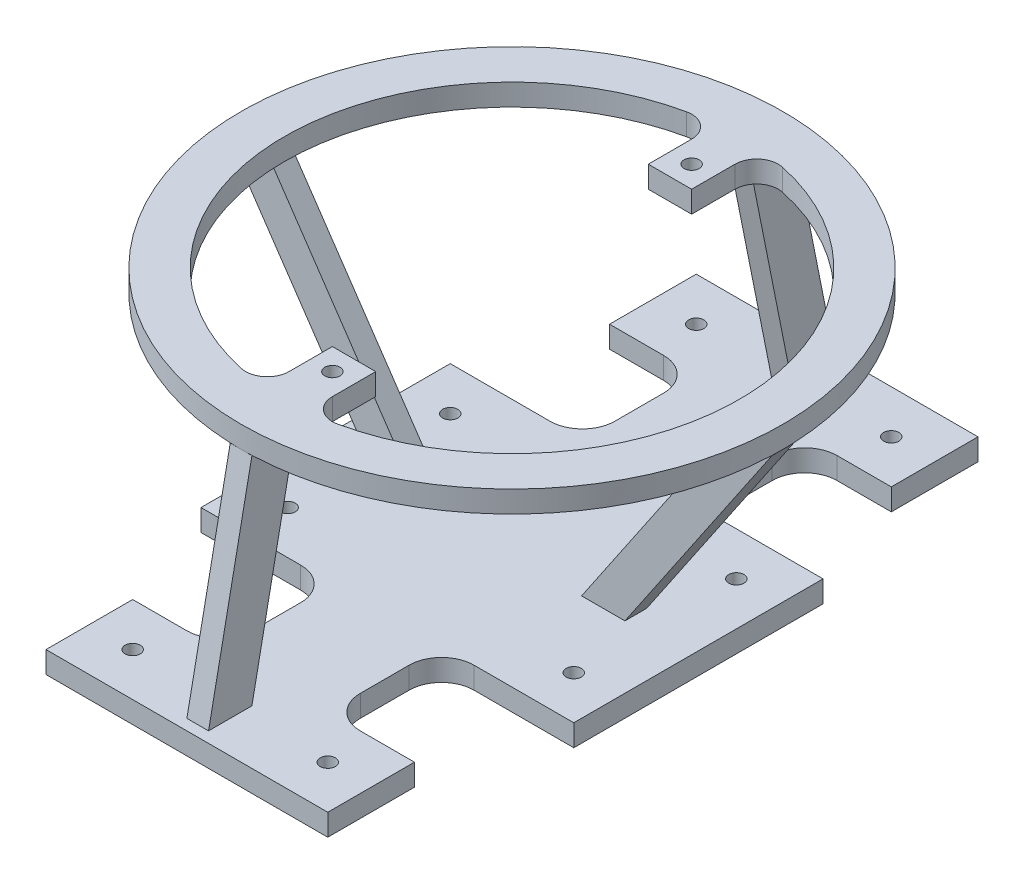
SolidWorks part; units mm, degrees
other "Detailelement1"
other "Detailelement2"
other "Detailelement4"
other "Detailelement8"
other "Detailelement10"
other "Detailelement12"
other "Detailelement14"
other "Detailelement15"
other "Detailelement16"
other "Schweißnaht-Ordner"
other "Schweißnaht1"
other "Schweißnaht2"
other "Schweißnaht4"
other "Schweißnaht14"
other "Schweißnaht15"
other "Schweißnaht16"
ref_plane "Ebene vorne" through (0, 0, 0) normal (0, 0, 1) x (1, 0, 0)
ref_plane "Ebene oben" through (0, 0, 0) normal (0, 1, 0) x (1, 0, 0)
ref_plane "Ebene rechts" through (0, 0, 0) normal (1, 0, 0) x (0, 0, -1)
sketch "Skizze1" plane through (0, 0, 0) normal (0, 1, 0) x (1, 0, 0)
  line L0 (75.8383, 35.8512) -> (145.8383, 35.8512)
  line L1 (-74.1617, 35.8512) -> (-4.1617, 35.8512)
  line L2 (-74.1617, 35.8512) -> (-74.1617, -79.1488)
  line L3 (-74.1617, -79.1488) -> (-4.1617, -79.1488)
  line L4 (145.8383, 35.8512) -> (145.8383, -79.1488)
  line L5 (75.8383, -79.1488) -> (145.8383, -79.1488)
  line L10 (60.8383, -94.1488) -> (60.8383, -191.6488)
  line L11 (10.8383, -94.1488) -> (10.8383, -191.6488)
  line L12 (60.8383, 148.3512) -> (10.8383, 148.3512)
  line L13 (60.8383, 148.3512) -> (60.8383, 50.8512)
  line L14 (60.8383, -191.6488) -> (10.8383, -191.6488)
  line L15 (10.8383, 148.3512) -> (10.8383, 50.8512)
  arc A0 (-4.1617, 35.8512) -> (10.8383, 50.8512) centre (-4.1617, 50.8512) ccw
  arc A1 (10.8383, -94.1488) -> (-4.1617, -79.1488) centre (-4.1617, -94.1488) ccw
  arc A2 (60.8383, -94.1488) -> (75.8383, -79.1488) centre (75.8383, -94.1488) cw
  arc A3 (60.8383, 50.8512) -> (75.8383, 35.8512) centre (75.8383, 50.8512) ccw
  point P18 (10.8383, -79.1488)
  point P21 (60.8383, -79.1488)
  dimension "D5" = 15
  dimension "D6" = 15
  dimension "D7" = 15
  dimension "D8" = 15
  dimension "D1" = 340
  dimension "D2" = 50
  dimension "D3" = 141.0009
  dimension "D4" = 242.8606
extrude "Aufsatz-Linear austragen1" add sketch "Skizze1" along normal blind 10
ref_plane "Ebene4" through (0, 0, 21.6488) normal (0, 0, 1) x (1, 0, 0)
ref_plane "Ebene5" through (0, 120, 0) normal (0, 1, 0) x (1, 0, 0)
sketch "Skizze4" plane through (0, 10, 0) normal (0, 1, 0) x (1, 0, 0)
  line L0 (145.8383, -21.6488) -> (-74.1617, -21.6488)
  line L1 (145.8383, 35.8512) -> (145.8383, -79.1488) construction
  line L2 (-74.1617, 35.8512) -> (-74.1617, -79.1488) construction
  line L3 (35.8383, -191.6488) -> (35.8383, 148.3512)
  line L4 (10.8383, -191.6488) -> (60.8383, -191.6488) construction
  line L5 (10.8383, 148.3512) -> (60.8383, 148.3512) construction
sketch "Skizze5" plane through (0, 0, 21.6488) normal (0, 0, 1) x (1, 0, 0)
  line L0 (35.8383, 10) -> (35.8383, 120)
  dimension "D1" = 110
  dimension "D2" = 155.5635
  dimension "D3" = 110
sketch "Skizze6" plane through (0, 120, 0) normal (0, 1, 0) x (1, 0, 0)
  line L7 (25.8383, 71.222) -> (25.8383, 51.222)
  line L8 (25.8383, 51.222) -> (45.8383, 51.222)
  line L9 (45.8383, 51.222) -> (45.8383, 71.222)
  line L10 (-74.9254, -21.6488) -> (74.9254, -21.6488) construction
  line L11 (45.8383, -94.5197) -> (45.8383, -114.5197)
  line L12 (25.8383, -94.5197) -> (45.8383, -94.5197)
  line L13 (25.8383, -114.5197) -> (25.8383, -94.5197)
  arc A0 (13.733, 80.9979) -> (13.733, -124.2956) centre (35.8383, -21.6488) ccw
  circle A1 centre (35.8383, -21.6488) radius 125
  arc A2 (13.733, 80.9979) -> (25.8383, 71.222) centre (15.8383, 71.222) cw
  arc A3 (57.9436, 80.9979) -> (45.8383, 71.222) centre (55.8383, 71.222) ccw
  arc A4 (57.9436, -124.2956) -> (45.8383, -114.5197) centre (55.8383, -114.5197) cw
  arc A5 (13.733, -124.2956) -> (25.8383, -114.5197) centre (15.8383, -114.5197) ccw
  arc A6 (57.9436, -124.2956) -> (57.9436, 80.9979) centre (35.8383, -21.6488) ccw
  dimension "D1" = 10
extrude "Aufsatz-Linear austragen2" add sketch "Skizze6" against normal blind 10 separate body
ref_plane "Ebene6" through (35.8383, 0, 0) normal (1, 0, 0) x (0, 0, -1)
sketch "Skizze7" plane through (35.8383, 0, 0) normal (1, 0, 0) x (0, 0, -1)
  line L0 (-146.6488, 110) -> (-126.6488, 110)
  line L1 (-126.6488, 110) -> (-146.6488, 10)
  line L2 (-191.6488, 10) -> (148.3512, 10) construction
  line L3 (-146.6488, 10) -> (-166.6488, 10)
  line L4 (-166.6488, 10) -> (-146.6488, 110)
  line L5 (-79.1488, 10) -> (-79.1488, 0) construction
  dimension "D1" = 11.31
  dimension "D2" = 101.9804
  dimension "D3" = 21.5728
extrude "Aufsatz-Linear austragen3" add sketch "Skizze7" along normal blind 5 and the other way blind 5
mirror "Spiegeln1" about plane through (0, 0, 21.6488) normal (0, 0, 1) of "Aufsatz-Linear austragen3"
sketch "Skizze8" plane through (0, 10, 0) normal (0, 1, 0) x (1, 0, 0)
  line L0 (10.8383, -94.1488) -> (10.8383, -191.6488) construction
  line L6 (60.8383, 148.3512) -> (10.8383, 148.3512)
  line L7 (60.8383, 148.3512) -> (60.8383, 128.3512)
  line L8 (60.8383, 128.3512) -> (10.8383, 128.3512)
  line L9 (10.8383, 148.3512) -> (10.8383, 128.3512)
  line L11 (60.8383, -191.6488) -> (10.8383, -191.6488)
  line L12 (60.8383, -191.6488) -> (60.8383, -171.6488)
  line L13 (60.8383, -171.6488) -> (10.8383, -171.6488)
  line L14 (10.8383, -191.6488) -> (10.8383, -171.6488)
  line L16 (-74.1617, -79.1488) -> (-4.1617, -79.1488) construction
  line L17 (-74.1617, 35.8512) -> (-4.1617, 35.8512) construction
  line L18 (-74.1617, 35.8512) -> (-74.1617, -79.1488) construction
  line L19 (145.8383, 35.8512) -> (145.8383, -79.1488) construction
  dimension "D1" = 92.5
  dimension "D2" = 92.5
  dimension "D3" = 85
  dimension "D4" = 112.5
  dimension "D5" = 85
extrude "Schnitt-Linear austragen1" cut sketch "Skizze8" against normal blind 10
sketch "Skizze9" plane through (0, 10, 0) normal (0, 1, 0) x (1, 0, 0)
  line L0 (-74.1617, 35.8512) -> (-74.1617, -79.1488) construction
  line L1 (10.8383, 128.3512) -> (-29.1617, 128.3512)
  line L2 (10.8383, 128.3512) -> (10.8383, 88.3512)
  line L3 (-4.1617, 88.3512) -> (-29.1617, 88.3512)
  line L4 (-29.1617, 128.3512) -> (-29.1617, 88.3512)
  line L5 (10.8383, -171.6488) -> (-29.1617, -171.6488)
  line L6 (10.8383, -171.6488) -> (10.8383, -131.6488)
  line L7 (-4.1617, -131.6488) -> (-29.1617, -131.6488)
  line L8 (-29.1617, -171.6488) -> (-29.1617, -131.6488)
  line L9 (60.8383, 128.3512) -> (100.8383, 128.3512)
  line L10 (60.8383, 128.3512) -> (60.8383, 88.3512)
  line L11 (75.8383, 88.3512) -> (100.8383, 88.3512)
  line L12 (100.8383, 128.3512) -> (100.8383, 88.3512)
  line L13 (60.8383, -171.6488) -> (100.8383, -171.6488)
  line L14 (60.8383, -171.6488) -> (60.8383, -131.6488)
  line L15 (75.8383, -131.6488) -> (100.8383, -131.6488)
  line L16 (100.8383, -171.6488) -> (100.8383, -131.6488)
  line L18 (40.8383, 103.3512) -> (40.8383, 123.3512) construction
  line L19 (-74.1617, 35.8512) -> (-4.1617, 35.8512) construction
  line L22 (75.8383, -79.1488) -> (145.8383, -79.1488) construction
  line L23 (10.8383, -94.1488) -> (10.8383, -171.6488) construction
  line L24 (10.8383, 128.3512) -> (10.8383, 50.8512) construction
  line L25 (75.8383, 35.8512) -> (145.8383, 35.8512) construction
  line L26 (10.8383, 73.3512) -> (10.8383, 69.0038)
  line L27 (60.8383, 73.3512) -> (60.8383, 69.0038)
  line L28 (60.8383, 128.3512) -> (60.8383, 50.8512) construction
  line L29 (60.8383, 88.3512) -> (60.8383, 73.3512)
  line L30 (10.8383, 88.3512) -> (10.8383, 69.0038)
  line L31 (10.8383, -116.6488) -> (10.8383, -111.5007)
  line L32 (10.8383, -131.6488) -> (10.8383, -111.5007)
  line L33 (60.8383, -116.6488) -> (60.8383, -111.5007)
  line L34 (60.8383, -94.1488) -> (60.8383, -171.6488) construction
  line L35 (60.8383, -111.5007) -> (60.8383, -131.6488)
  arc A0 (10.8383, 73.3512) -> (-4.1617, 88.3512) centre (-4.1617, 73.3512) ccw
  arc A1 (60.8383, 73.3512) -> (75.8383, 88.3512) centre (75.8383, 73.3512) cw
  arc A2 (-4.1617, -131.6488) -> (10.8383, -116.6488) centre (-4.1617, -116.6488) ccw
  arc A3 (75.8383, -131.6488) -> (60.8383, -116.6488) centre (75.8383, -116.6488) cw
  line M39 (60.8383, -171.6488) -> (60.8383, -94.1488)
  line M44 (60.8383, 50.8512) -> (60.8383, 128.3512)
  line M45 (10.8383, 128.3512) -> (10.8383, 50.8512)
  line M48 (10.8383, -94.1488) -> (10.8383, -171.6488)
  dimension "D17" = 15
  dimension "D18" = 15
  dimension "D19" = 15
  dimension "D20" = 15
  dimension "D1" = 40
  dimension "D2" = 40
  dimension "D3" = 40
  dimension "D4" = 40
  dimension "D5" = 90
  dimension "D6" = 45
  dimension "D7" = 45
  dimension "D8" = 60
  dimension "D9" = 220
  dimension "D10" = 92.5
  dimension "D11" = 85
  dimension "D12" = 52.5
  dimension "D13" = 90
  dimension "D14" = 50
  dimension "D15" = 50
  dimension "D16" = 52.5
extrude "Aufsatz-Linear austragen4" add sketch "Skizze9" against normal blind 10 contours L15 A3 L13 L16 M39 | A2 L7 L8 L5 M48 | A1 L11 L12 L9 M44 | A0 L1 L4 L3 M45
sketch "Skizze14" plane through (0, 10, 0) normal (0, 1, 0) x (1, 0, 0)
  line L0 (-74.1617, -79.1488) -> (-4.1617, -79.1488) construction
  line L1 (145.8383, 35.8512) -> (121.8383, 35.8512)
  line L2 (145.8383, 35.8512) -> (145.8383, -79.1488)
  line L3 (145.8383, -79.1488) -> (121.8383, -79.1488)
  line L4 (121.8383, 35.8512) -> (121.8383, -79.1488)
  line L9 (60.8383, 73.3512) -> (60.8383, 50.8512) construction
  arc A0 (10.8383, -94.1488) -> (-4.1617, -79.1488) centre (-4.1617, -94.1488) ccw construction
  dimension "D1" = 150
  dimension "D2" = 61
  dimension "D3" = 15
extrude "Schnitt-Linear austragen2" cut sketch "Skizze14" against normal blind 10
sketch "Skizze15" plane through (0, 10, 0) normal (0, 1, 0) x (1, 0, 0)
  line L0 (-74.1617, 35.8512) -> (-4.1617, 35.8512) construction
  line L1 (-74.1617, -79.1488) -> (-50.1617, -79.1488)
  line L2 (-74.1617, -79.1488) -> (-74.1617, 35.8512)
  line L3 (-74.1617, 35.8512) -> (-50.1617, 35.8512)
  line L4 (-50.1617, -79.1488) -> (-50.1617, 35.8512)
extrude "Schnitt-Linear austragen3" cut sketch "Skizze15" against normal blind 10
sketch "Skizze16" plane through (0, 0, 21.6488) normal (0, 0, 1) x (1, 0, 0)
  line L0 (-89.1617, 110) -> (-69.1617, 110)
  line L1 (-69.1617, 110) -> (0, 8.1353)
  line L2 (0, 8.1353) -> (-20, 8.1353)
  line L3 (-20, 8.1353) -> (-89.1617, 110)
  line L4 (-50.1617, 10) -> (-4.1617, 10) construction
  dimension "D1" = 123.125
  dimension "D2" = 124.175
extrude "Aufsatz-Linear austragen8" add sketch "Skizze16" along normal blind 5 and the other way blind 5 contours L3 L0 L1 L2
mirror "Spiegeln5" about plane through (35.8383, 0, 0) normal (1, 0, 0) of "Aufsatz-Linear austragen8"
sketch "Skizze22" plane through (0, 110, 0) normal (0, -1, 0) x (-1, 0, 0)
  line L0 (-25.8383, 51.222) -> (-25.8383, 61.222)
  line L1 (-25.8383, 51.222) -> (-25.8383, 71.222) construction
  line L2 (-25.8383, 61.222) -> (-35.8383, 61.222)
  line L3 (-25.8383, -94.5197) -> (-25.8383, -104.5197)
  line L4 (-25.8383, -114.5197) -> (-25.8383, -94.5197) construction
  line L5 (-25.8383, -104.5197) -> (-35.8383, -104.5197)
hole_wizard "Kernloch für M8x1.0 Gewinde2" positions "3D-Skizze2" profile "Skizze23" hole size "M8x1.0" standard "DIN"
sketch3d "3D-Skizze2"
  point P0 (35.8383, 110, -61.222)
  point P3 (35.8383, 110, 104.5197)
sketch "Skizze23" plane through (35.8383, 110, -61.222) normal (1, 0, 0) x (0, 0, -1)
  line L0 (0, 0) -> (0, 22.103)
  line L1 (0, 22.103) -> (3.5, 20)
  line L2 (3.5, 20) -> (3.5, 0)
  line L5 (3.5, 0) -> (0, 0)
  line L10 (0, 22.103) -> (-3.5, 20) construction
  line L11 (0, -6.35) -> (0, 107.95) construction
  dimension "Bohrerdurchmesser" = 7
  dimension "Bohrungstiefe" = 20
  dimension "Spitzenwinkel" = 118
sketch "Skizze24" plane through (0, 10, 0) normal (0, 1, 0) x (1, 0, 0)
  line L0 (35.8383, 128.3512) -> (35.8383, -179.717)
  line L1 (-29.1617, 128.3512) -> (100.8383, 128.3512) construction
  line L2 (-29.1617, 128.3512) -> (-29.1617, 108.3512)
  line L3 (-29.1617, 128.3512) -> (-29.1617, 88.3512) construction
  line L4 (100.8383, 128.3512) -> (100.8383, 108.3512)
  line L5 (-29.1617, 108.3512) -> (-9.1617, 108.3512)
  line L6 (100.8383, 108.3512) -> (80.8383, 108.3512)
  line L7 (-50.1617, 35.8512) -> (-50.1617, 15.8512)
  line L8 (-50.1617, -79.1488) -> (-50.1617, 35.8512) construction
  line L9 (121.8383, 35.8512) -> (121.8383, 15.8512)
  line L10 (-50.1617, 15.8512) -> (-30.1617, 15.8512)
  line L11 (121.8383, 15.8512) -> (101.8383, 15.8512)
  line L12 (-50.1617, -79.1488) -> (-50.1617, -59.1488)
  line L13 (121.8383, -79.1488) -> (121.8383, -59.1488)
  line L14 (-50.1617, -59.1488) -> (-30.1617, -59.1488)
  line L15 (121.8383, -59.1488) -> (101.8383, -59.1488)
  line L16 (-29.1617, -171.6488) -> (-29.1617, -151.6488)
  line L17 (-29.1617, -171.6488) -> (-29.1617, -131.6488) construction
  line L18 (100.8383, -171.6488) -> (100.8383, -151.6488)
  line L19 (-29.1617, -151.6488) -> (-9.1617, -151.6488)
  line L20 (100.8383, -151.6488) -> (80.8383, -151.6488)
  point P38 (-40.1617, 15.8512)
  point P39 (0, 0)
  dimension "D1" = 75
  dimension "D2" = 112.5
hole_wizard "Kernloch für M8x1.0 Gewinde3" positions "3D-Skizze3" profile "Skizze25" hole size "M8x1.0" standard "DIN"
sketch3d "3D-Skizze3"
  point P0 (101.8383, 10, -15.8512)
  point P3 (101.8383, 10, 59.1488)
  point P6 (-30.1617, 10, -15.8512)
  point P9 (-9.1617, 10, -108.3512)
  point P12 (-30.1617, 10, 59.1488)
  point P15 (-9.1617, 10, 151.6488)
  point P18 (80.8383, 10, 151.6488)
  point P21 (80.8383, 10, -108.3512)
sketch "Skizze25" plane through (101.8383, 10, -15.8512) normal (1, 0, 0) x (0, 0, 1)
  line L0 (0, 0) -> (0, 22.103)
  line L1 (0, 22.103) -> (3.5, 20)
  line L2 (3.5, 20) -> (3.5, 0)
  line L5 (3.5, 0) -> (0, 0)
  line L10 (0, 22.103) -> (-3.5, 20) construction
  line L11 (0, -6.35) -> (0, 107.95) construction
  dimension "Bohrerdurchmesser" = 7
  dimension "Bohrungstiefe" = 20
  dimension "Spitzenwinkel" = 118
